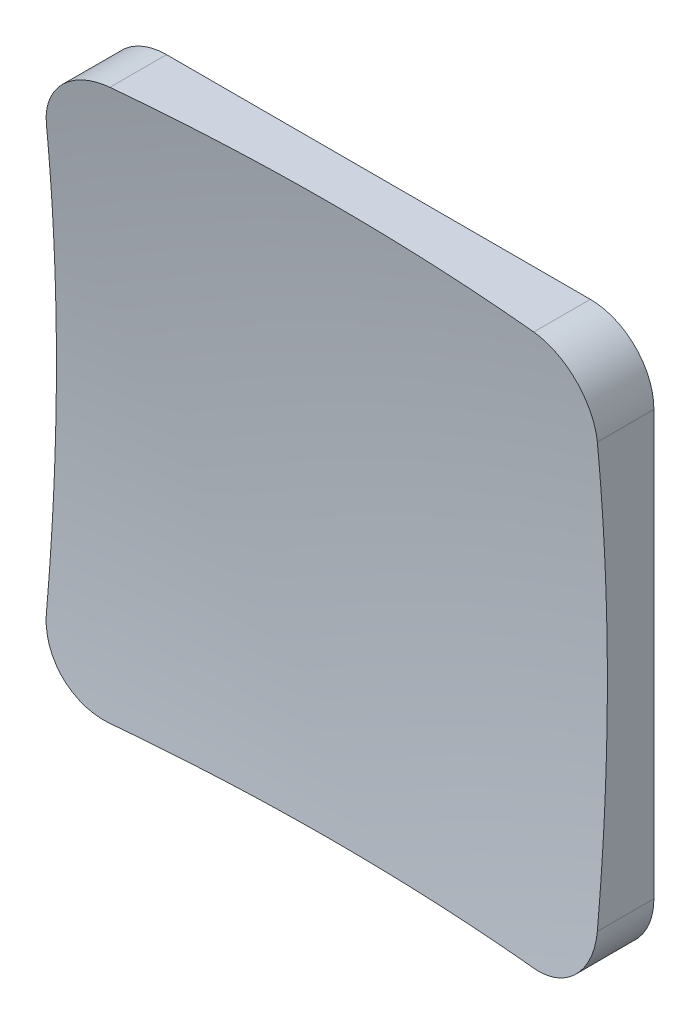
SolidWorks part; units mm, degrees
ref_plane "Płaszczyzna przednia" through (0, 0, 0) normal (0, 0, 1) x (1, 0, 0)
ref_plane "Płaszczyzna górna" through (0, 0, 0) normal (0, 1, 0) x (1, 0, 0)
ref_plane "Płaszczyzna prawa" through (0, 0, 0) normal (1, 0, 0) x (0, 0, -1)
sketch "Sketch1" plane through (0, 0, 0) normal (0, 0, 1) x (1, 0, 0)
  line L1 (-65, -65) -> (65, -65)
  line L2 (-65, -65) -> (-65, 65)
  line L3 (-65, 65) -> (65, 65)
  line L4 (65, -65) -> (65, 65)
  line L5 (-65, -65) -> (65, 65) construction
  line L6 (-65, 65) -> (65, -65) construction
  point P0 (0, 0)
  dimension "D1" = 130
  dimension "D2" = 130
extrude "Boss-Extrude1" add sketch "Sketch1" along normal blind 15
fillet "Fillet1" radius 15 4 edges at (65, -65, 7.5) (-65, -65, 7.5) (-65, 65, 7.5) (65, 65, 7.5)
sketch "Sketch5" plane through (0, 0, 15) normal (0, 0, 1) x (1, 0, 0)
  line L0 (-65, 65) -> (65, -65)
  line L1 (-65, -65) -> (65, -65) construction
  line L2 (-65, -65) -> (-65, 65) construction
  line L3 (-65, 65) -> (65, 65) construction
  line L4 (65, -65) -> (65, 65) construction
  line L5 (-65, -65) -> (65, 65) construction
  line L6 (-65, 65) -> (65, -65) construction
  line L7 (65, -65) -> (70.5042, -59.4958)
  line L8 (70.5042, -59.4958) -> (-59.4958, 70.5042)
  line L9 (-59.4958, 70.5042) -> (-65, 65)
  point P0 (0, 0)
  point P1 (0, 0)
  dimension "D1" = 130
  dimension "D2" = 130
extrude "Boss-Extrude3" add sketch "Sketch5" along normal blind 20
sketch "Sketch6" plane through (0, 0, 0) normal (-0.7071, -0.7071, 0) x (0, 0, 1)
  line L11 (45.8826, 0) -> (539, 0) construction
  line L12 (15, 91.9239) -> (15, 99.5144)
  line L13 (15, 99.5144) -> (45.8826, 99.5144)
  line L14 (45.8826, 99.5144) -> (45.8826, 91.9239)
  line L18 (45.8826, 0) -> (6.9981, 0)
  line L20 (45.8826, 91.9239) -> (45.8826, 0)
  arc A0 (6.9981, 0) -> (15, 91.9239) centre (539, 0) cw
  point P11 (45.8826, 0)
revolve "Cut-Revolve2" cut sketch "Sketch6" angle 360 about L11
sketch "Sketch7" plane through (0, 0, 0) normal (0, 0, -1) x (-1, 0, 0)
  line L0 (-50, 65) -> (50, 65) construction
  line L1 (-22, -65) -> (22, -65)
  line L2 (-22, -65) -> (-22, -22)
  line L3 (-22, 65) -> (22, 65)
  line L4 (22, -65) -> (22, -22)
  line L7 (65, 50) -> (65, -50) construction
  line L8 (-65, -22) -> (-22, -22)
  line L9 (-65, -22) -> (-65, 22)
  line L10 (-65, 22) -> (-22, 22)
  line L11 (65, -22) -> (65, 22)
  line L12 (22, -22) -> (65, -22)
  line L14 (-22, 22) -> (-22, 65)
  line L16 (22, 22) -> (65, 22)
  line L17 (22, 22) -> (22, 65)
  point P0 (0, 0)
  point P8 (-14.7231, -43.5)
  dimension "D1" = 44
  dimension "D2" = 44
extrude "Boss-Extrude4" add sketch "Sketch7" along normal blind 23
sketch "Sketch8" plane through (0, -22, 0) normal (0, -1, 0) x (1, 0, 0)
  line L0 (0, 0) -> (0, -23) construction
  line L1 (22, -23) -> (-22, -23) construction
  line L2 (0, -23) -> (40, -23) construction
  line L3 (65, -23) -> (22, -23) construction
  line L4 (0, -23) -> (-40, -23) construction
  line L5 (-22, -23) -> (-65, -23) construction
  line L6 (-65, 0) -> (-65, -20) construction
  line L7 (-65, -23) -> (-65, 0) construction
  line L8 (-65, -20) -> (-45, -20) construction
  line L9 (-65, 0) -> (-45, -20) construction
  line L10 (-45, -20) -> (-42, -23) construction
  line L11 (-42, -23) -> (-40, -23) construction
  line L12 (65, 0) -> (65, -23) construction
  line L13 (65, -23) -> (42, -23) construction
  line L14 (42, -23) -> (65, 0) construction
  line L15 (65, 0) -> (55.8076, -9.1924) construction
  line L16 (-65, 0) -> (-55.8076, -9.1924) construction
  line L17 (-55.8076, -9.1924) -> (-45.8076, -9.1924) construction
  line L18 (55.8076, -9.1924) -> (45.8076, -9.1924) construction
  line L19 (45.8076, -9.1924) -> (40, -23) construction
  line L20 (-45.8076, -9.1924) -> (-40, -23) construction
  line L21 (-65, 0) -> (-55.8076, -9.1924)
  line L22 (-55.8076, -9.1924) -> (-45.8076, -9.1924)
  line L23 (-45.8076, -9.1924) -> (-40, -23)
  line L24 (-40, -23) -> (0, -40.62)
  line L25 (0, -40.62) -> (40, -23)
  line L26 (40, -23) -> (45.8076, -9.1924)
  line L27 (45.8076, -9.1924) -> (55.8076, -9.1924)
  line L28 (55.8076, -9.1924) -> (65, 0)
  line L29 (65, 0) -> (68.212, -1.351)
  line L30 (68.212, -1.351) -> (68.6827, -47.4988)
  line L31 (68.6827, -47.4988) -> (-34.3381, -46.2669)
  line L32 (-34.3381, -46.2669) -> (-70.1409, -27.5524)
  line L33 (-70.1409, -27.5524) -> (-65, 0)
  dimension "D1" = 40
  dimension "D2" = 40
  dimension "D3" = 23
  dimension "D4" = 13
  dimension "D5" = 13
extrude "Cut-Extrude1" cut sketch "Sketch8" against normal blind 50
sketch "Sketch9" plane through (22, 0, 0) normal (1, 0, 0) x (0, 0, -1)
  line L0 (0, 65) -> (20, 65) construction
  line L1 (23, 65) -> (0, 65) construction
  line L2 (20, 65) -> (20, 45) construction
  line L3 (0, 50) -> (0, 65) construction
  line L4 (0, 65) -> (20, 45) construction
  line L5 (0, 65) -> (9.1924, 55.8076) construction
  line L6 (9.1924, 55.8076) -> (9.1924, 45.8076) construction
  line L7 (0, 0) -> (23, 0) construction
  line L8 (0, 22) -> (0, -22) construction
  line L9 (23, 22) -> (23, -22) construction
  line L10 (23, 0) -> (23, 40) construction
  line L11 (23, 65) -> (23, 22) construction
  line L12 (9.1924, 45.8076) -> (23, 40) construction
  line L13 (0, 65) -> (9.1924, 55.8076)
  line L14 (9.1924, 55.8076) -> (9.1924, 45.8076)
  line L15 (9.1924, 45.8076) -> (23, 40)
  line L16 (23, 40) -> (23, 65)
  line L17 (23, 65) -> (0, 65)
  dimension "D1" = 20
  dimension "D2" = 20
  dimension "D3" = 13
extrude "Cut-Extrude2" cut sketch "Sketch9" against normal blind 50
sketch "Sketch10" plane through (0, -65, 0) normal (0, -1, 0) x (1, 0, 0)
  line L0 (0, 0) -> (0, -3) construction
  circle A0 centre (0, -3) radius 3
extrude "Cut-Extrude3" cut sketch "Sketch10" against normal blind 10
